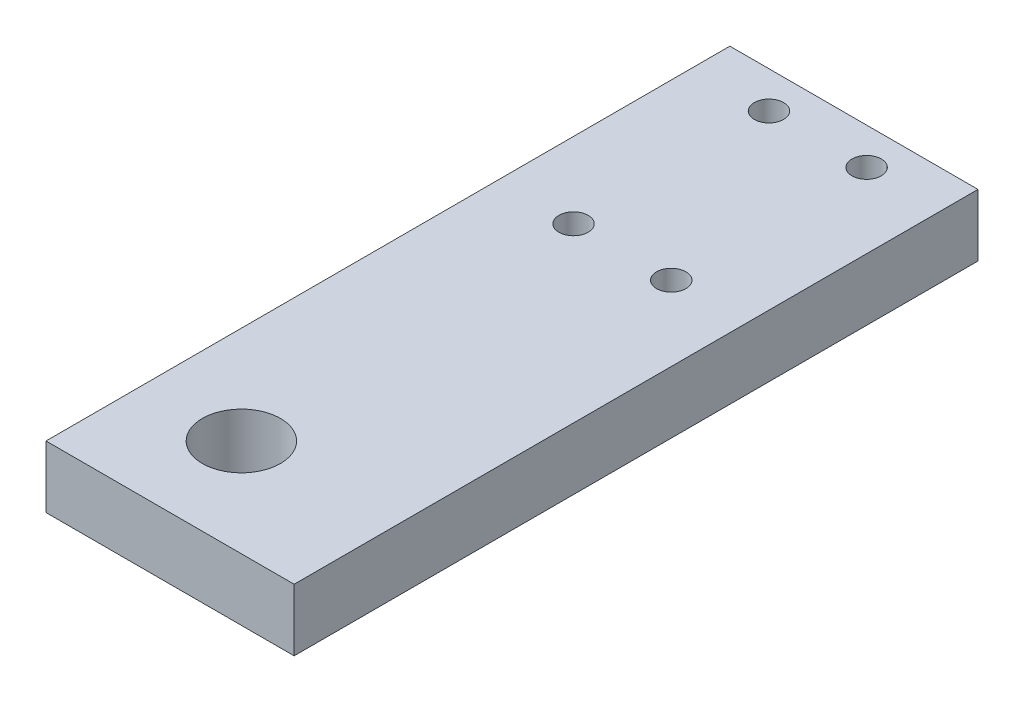
SolidWorks part; units mm, degrees
ref_plane "Front Plane" through (0, 0, 0) normal (0, 0, 1) x (1, 0, 0)
ref_plane "Top Plane" through (0, 0, 0) normal (0, 1, 0) x (1, 0, 0)
ref_plane "Right Plane" through (0, 0, 0) normal (1, 0, 0) x (0, 0, -1)
sketch "Sketch2" plane through (0, 0, 0) normal (0, 1, 0) x (1, 0, 0)
  line L1 (0, 0) -> (101.6, 0)
  line L2 (0, 0) -> (0, 280)
  line L3 (0, 280) -> (101.6, 280)
  line L4 (101.6, 0) -> (101.6, 280)
  dimension "D1" = 101.6
  dimension "D2" = 280
extrude "Boss-Extrude1" add sketch "Sketch2" along normal blind 25.4
sketch "Sketch3" plane through (0, 25.4, 0) normal (0, 1, 0) x (1, 0, 0)
  line L1 (0, 280) -> (51, 280)
  line L2 (0, 280) -> (0, 225)
  line L3 (0, 225) -> (51, 225)
  line L4 (51, 280) -> (51, 225)
  line L5 (31, 185) -> (71, 185)
  line L6 (31, 185) -> (31, 265)
  line L7 (31, 265) -> (71, 265)
  line L8 (71, 185) -> (71, 265)
  line L9 (31, 185) -> (71, 265) construction
  line L10 (31, 265) -> (71, 185) construction
  circle A0 centre (71, 265) radius 6
  circle A1 centre (31, 265) radius 6
  circle A2 centre (31, 185) radius 6
  circle A3 centre (71, 185) radius 6
  dimension "D1" = 51
  dimension "D2" = 55
  dimension "D3" = 40
  dimension "D4" = 80
extrude "Cut-Extrude1" cut sketch "Sketch3" against normal blind 25.4 contours A1 | A0 | A3 | A2
sketch "Sketch4" plane through (0, 25.4, 0) normal (0, 1, 0) x (1, 0, 0)
  line L1 (0, 280) -> (40, 280)
  line L2 (0, 280) -> (0, 40)
  line L3 (0, 40) -> (40, 40)
  line L4 (40, 280) -> (40, 40)
  circle A0 centre (40, 40) radius 16
  dimension "D1" = 240
  dimension "D2" = 40
extrude "Cut-Extrude2" cut sketch "Sketch4" against normal blind 25.4 contours A0
